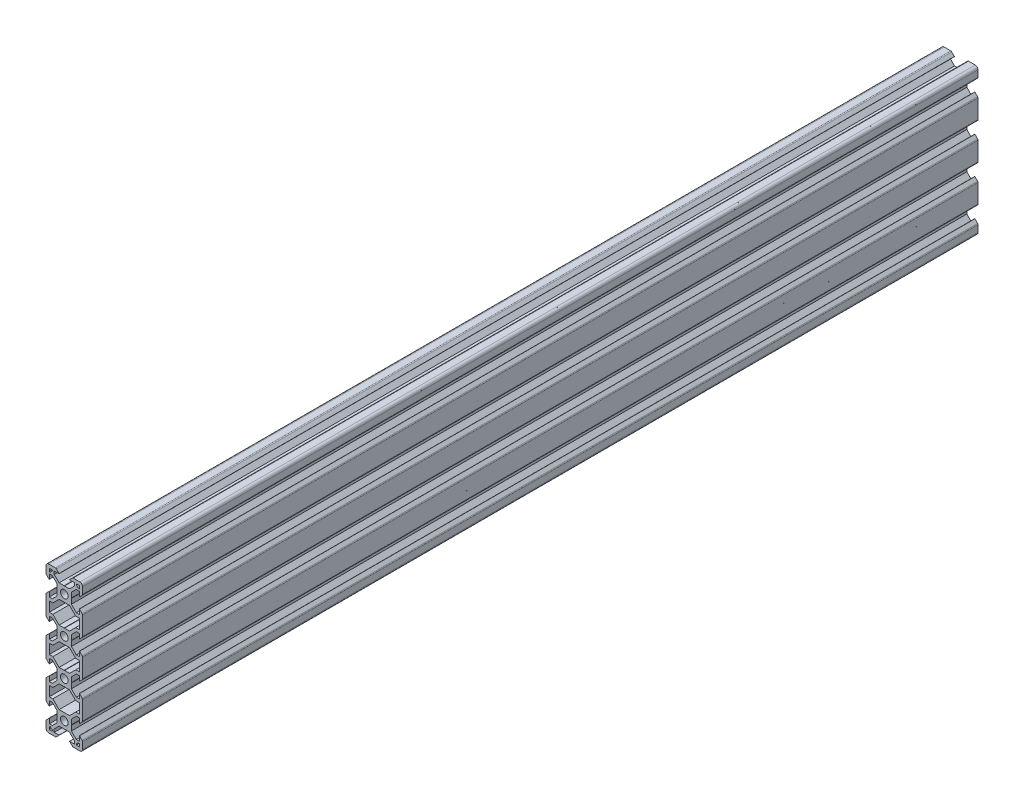
SolidWorks part; units mm, degrees
material "6063-T5"
ref_plane "Front Plane" through (0, 0, 0) normal (0, 0, 1) x (1, 0, 0)
ref_plane "Top Plane" through (0, 0, 0) normal (0, 1, 0) x (1, 0, 0)
ref_plane "Right Plane" through (0, 0, 0) normal (1, 0, 0) x (0, 0, -1)
sketch "Sketch2" plane through (0, 0, 0) normal (0, 0, 1) x (1, 0, 0)
  line L0 (-8.2, 2.8875) -> (-8.2, 5.4975)
  line L3 (-4.9072, 9.9975) -> (-8.5, 9.9975)
  line L4 (-10, 4.9047) -> (-10, 8.4975)
  line L5 (-2.1, 0) -> (-3.8, 0) construction
  line L6 (0, 3.8) -> (0, 2.1) construction
  line L7 (-0.1, 3.9) -> (-2.8404, 3.9)
  line L8 (-3.9, 0.1) -> (-3.9, 2.8383)
  line L9 (-2.89, 8.1975) -> (-5.5, 8.1975)
  line L10 (-6.57, 8.1975) -> (-6.57, 7.6575)
  line L11 (-8.2, 6.5675) -> (-7.66, 6.5675)
  line L12 (-5.5, 8.1975) -> (-5.5, 6.5588)
  line L13 (-6.56, 5.4975) -> (-8.2, 5.4975)
  line L14 (-8.2, 8.1975) -> (-1.4852, 1.4847) construction
  line L15 (-6.56, 5.4975) -> (-3.9, 2.8383)
  line L16 (-5.5, 6.5588) -> (-2.8404, 3.9)
  line L17 (-7.66, 6.5675) -> (-6.57, 7.6575)
  line L18 (-8.7302, 7.6671) -> (-0.5302, -0.5304) construction
  line L19 (-7.6698, 8.7279) -> (0.5302, 0.5304) construction
  line L20 (-8.2, 8.1975) -> (0, 0) construction
  line L21 (-8.2, 6.5675) -> (-8.2, 8.1975)
  line L22 (-8.2, -0.0025) -> (-8.2, 8.1975) construction
  line L23 (-6.57, 8.1975) -> (-8.2, 8.1975)
  line L24 (0, 8.1975) -> (-8.2, 8.1975) construction
  line L25 (-10, -0.0025) -> (-10, 9.9975) construction
  line L26 (0, 9.9975) -> (-10, 9.9975) construction
  line L27 (-2.89, 8.3075) -> (-2.89, 8.1975)
  line L29 (-8.31, 2.8875) -> (-8.2, 2.8875)
  line L30 (-4.3486, 9.7661) -> (-2.89, 8.3075)
  line L31 (-8.31, 2.8875) -> (-9.7686, 4.3461)
  line L34 (-0.1, 3.9) -> (0, 3.8)
  line L35 (-3.9, 0.1) -> (-3.8, 0)
  line L36 (-10, -20) -> (0, -20) construction
  line L37 (0, 0) -> (0, -20) construction
  line L38 (0, -3.9) -> (-2.8404, -3.9)
  line L39 (-3.8, 0) -> (-3.9, -0.1)
  line L40 (-3.9, -0.1) -> (-3.9, -2.84)
  line L41 (-2.8404, -3.9) -> (-6.25, -7.3096)
  line L42 (-3.9, -2.84) -> (-6.56, -5.5)
  line L43 (-8.21, -2.89) -> (-8.21, -5.5)
  line L44 (-6.56, 5.4975) -> (-6.56, -5.5) construction
  line L45 (-6.56, -5.5) -> (-8.21, -5.5)
  line L46 (-6.25, -7.3096) -> (-6.25, -12.7) construction
  line L47 (-6.25, -7.3096) -> (-8.21, -7.3096)
  line L48 (-8.21, -2.89) -> (-8.31, -2.89)
  line L49 (-8.31, -2.89) -> (-9.7657, -4.3457)
  line L51 (-8.21, -7.3096) -> (-8.21, -12.7)
  line L52 (-0.1, -16.1) -> (-2.85, -16.1)
  line L53 (-3.9, -17.16) -> (-3.9, -19.9)
  line L54 (-6.25, -12.7) -> (-2.85, -16.1)
  line L58 (-3.9, -17.16) -> (-6.56, -14.5)
  line L60 (-8.21, -17.11) -> (-8.31, -17.11)
  line L61 (-10, -4.9114) -> (-10, -15.0886)
  line L62 (-9.7657, -15.6543) -> (-8.31, -17.11)
  line L63 (-0.1, -16.1) -> (0, -16.2)
  line L64 (-3.9, -19.9) -> (-3.8, -20)
  line L65 (-8.21, -14.5) -> (-6.56, -14.5)
  line L66 (-8.21, -12.7) -> (-6.25, -12.7)
  line L67 (-10, -30.01) -> (0, -30.01) construction
  line L68 (-8.21, -14.5) -> (-8.21, -17.11)
  line L69 (-3.9, -20.1) -> (-3.8, -20)
  line L71 (-10, -20) -> (0, -20) construction
  line L72 (-8.21, -30.01) -> (-8.21, -27.31)
  line L73 (-10, -30.01) -> (-10, -24.9101)
  line L74 (-8.21, -25.4987) -> (-8.21, -22.8887)
  line L76 (-8.21, -27.31) -> (-6.25, -27.31)
  line L77 (-8.21, -25.4987) -> (-6.56, -25.4987)
  line L85 (-0.1, -23.9) -> (0, -23.8)
  line L95 (-9.7657, -24.3444) -> (-8.31, -22.8887)
  line L96 (-8.21, -22.8887) -> (-8.31, -22.8887)
  line L97 (-3.9, -22.8387) -> (-6.56, -25.4987)
  line L98 (-6.25, -27.31) -> (-2.84, -23.9)
  line L99 (-3.9, -22.8387) -> (-3.9, -20.1)
  line L100 (-0.1, -23.9) -> (-2.84, -23.9)
  arc A1 (-10, 8.4975) -> (-8.5, 9.9975) centre (-8.5, 8.4975) cw
  arc A2 (-9.7686, 4.3461) -> (-10, 4.9047) centre (-9.21, 4.9047) cw
  arc A3 (-4.3486, 9.7661) -> (-4.9072, 9.9975) centre (-4.9072, 9.2075) ccw
  arc A5 (0, 2.1) -> (0, -2.1) centre (0, 0) ccw
  arc A6 (-9.7657, -15.6543) -> (-10, -15.0886) centre (-9.2, -15.0886) cw
  arc A7 (-9.7657, -4.3457) -> (-10, -4.9114) centre (-9.2, -4.9114) ccw
  arc A8 (0, -17.9) -> (0, -22.1) centre (0, -20) ccw
  arc A10 (-9.7657, -24.3444) -> (-10, -24.9101) centre (-9.2, -24.9101) ccw
  point P29 (-10, 9.9975)
  point P39 (-10, 4.5775)
  point P42 (-4.58, 9.9975)
  point P76 (-10, -15.42)
  point P79 (-10, -4.58)
  dimension "D15" = 1.5
  dimension "D22" = 0.79
  dimension "D30" = 2.1
  dimension "D31" = 2.1
  dimension "D51" = 0.8
  dimension "D52" = 2.61
  dimension "D64" = 1.65
  dimension "D53" = 0.8
  dimension "D55" = 3.9
  dimension "D4" = 1.8
  dimension "D5" = 3.43
  dimension "D6" = 3.43
  dimension "D7" = 0.54
  dimension "D8" = 0.54
  dimension "D9" = 1.07
  dimension "D10" = 1.07
  dimension "D11" = 3.9
  dimension "D12" = 3.9
  dimension "D16" = 7.11
  dimension "D17" = 0.11
  dimension "D18" = 1.69
  dimension "D19" = 0.11
  dimension "D20" = 7.11
  dimension "D21" = 1.69
  dimension "D23" = 10
  dimension "D24" = 0.1
  dimension "D25" = 45
  dimension "D26" = 0.1
  dimension "D27" = 45
  dimension "D28" = 1.64
  dimension "D29" = 20
  dimension "D32" = 3.9
  dimension "D33" = 45
  dimension "D34" = 2.74
  dimension "D35" = 45
  dimension "D36" = 1.96
  dimension "D37" = 2.61
  dimension "D38" = 90
  dimension "D39" = 2.61
  dimension "D40" = 3.9
  dimension "D41" = 3.9
  dimension "D42" = 135
  dimension "D44" = 45
  dimension "D45" = 1.8
  dimension "D46" = 0.1
  dimension "D47" = 0.1
  dimension "D48" = 45
  dimension "D49" = 0.1
  dimension "D50" = 45
  dimension "D43" = 5.5
  dimension "D54" = 3.9
  dimension "D56" = 45
  dimension "D57" = 2.7
  dimension "D59" = 45
  dimension "D60" = 0.1
  dimension "D61" = 0.1
  dimension "D62" = 45
  dimension "D63" = 2.84
  dimension "D65" = 1.96
  dimension "D66" = 45
  dimension "D67" = 1.5
  dimension "D13" = 0.75
  dimension "D14" = 0.75
sketch "Sketch3" plane through (0, 0, 0) normal (0, 0, 1) x (1, 0, 0)
  line L0 (-0.1, 3.9) -> (0, 3.8) construction
  line L1 (-0.1, 3.9) -> (-2.8404, 3.9) construction
  line L2 (-5.5, 6.5588) -> (-2.8404, 3.9) construction
  line L3 (-5.5, 8.1975) -> (-5.5, 6.5588) construction
  line L4 (-2.89, 8.1975) -> (-5.5, 8.1975) construction
  line L5 (-7.66, 6.5675) -> (-6.57, 7.6575)
  line L6 (-6.57, 7.6575) -> (-6.57, 8.1975)
  line L7 (-6.57, 8.1975) -> (-8.2, 8.1975)
  line L8 (-8.2, 8.1975) -> (-8.2, 6.5675)
  line L9 (-8.2, 6.5675) -> (-7.66, 6.5675)
  line L10 (-7.66, 6.5675) -> (-6.57, 7.6575)
  line L11 (-6.57, 7.6575) -> (-6.57, 8.1975)
  line L12 (-6.57, 8.1975) -> (-8.2, 8.1975)
  line L13 (-8.2, 8.1975) -> (-8.2, 6.5675)
  line L14 (-8.2, 6.5675) -> (-7.66, 6.5675)
  line L15 (-2.89, 8.3075) -> (-2.89, 8.1975) construction
  line L16 (-4.3486, 9.7661) -> (-2.89, 8.3075) construction
  line L17 (-4.9072, 9.9975) -> (-8.5, 9.9975) construction
  line L18 (-10, 4.9047) -> (-10, 8.4975) construction
  line L19 (-8.31, 2.8875) -> (-9.7686, 4.3461) construction
  line L20 (-8.31, 2.8875) -> (-8.2, 2.8875) construction
  line L21 (-8.2, 2.8875) -> (-8.2, 5.4975) construction
  line L22 (-6.56, 5.4975) -> (-8.2, 5.4975) construction
  line L23 (-6.56, 5.4975) -> (-3.9, 2.8383) construction
  line L24 (-3.9, 0.1) -> (-3.9, 2.8383) construction
  line L25 (-3.9, 0.1) -> (-3.8, 0) construction
  line L26 (-3.8, 0) -> (-3.9, -0.1) construction
  line L27 (-3.9, -0.1) -> (-3.9, -2.84) construction
  line L28 (-3.9, -2.84) -> (-6.56, -5.5) construction
  line L29 (-6.56, -5.5) -> (-8.21, -5.5) construction
  line L30 (-8.21, -2.89) -> (-8.21, -5.5) construction
  line L31 (-8.21, -2.89) -> (-8.31, -2.89) construction
  line L32 (-8.31, -2.89) -> (-9.7657, -4.3457) construction
  line L33 (-10, -4.9114) -> (-10, -15.0886) construction
  line L34 (-9.7657, -15.6543) -> (-8.31, -17.11) construction
  line L35 (-8.21, -17.11) -> (-8.31, -17.11) construction
  line L36 (-8.21, -14.5) -> (-8.21, -17.11) construction
  line L37 (-8.21, -14.5) -> (-6.56, -14.5) construction
  line L38 (-3.9, -17.16) -> (-6.56, -14.5) construction
  line L39 (-3.9, -17.16) -> (-3.9, -19.9) construction
  line L40 (-3.9, -19.9) -> (-3.8, -20) construction
  line L41 (-3.9, -20.1) -> (-3.8, -20) construction
  line L42 (-3.9, -22.8387) -> (-3.9, -20.1) construction
  line L43 (-3.9, -22.8387) -> (-6.56, -25.4987) construction
  line L44 (-8.21, -25.4987) -> (-6.56, -25.4987) construction
  line L45 (-8.21, -25.4987) -> (-8.21, -22.8887) construction
  line L46 (-8.21, -22.8887) -> (-8.31, -22.8887) construction
  line L47 (-9.7657, -24.3444) -> (-8.31, -22.8887) construction
  line L48 (-10, -30.01) -> (-10, -24.9101) construction
  line L49 (0, -3.9) -> (-2.8404, -3.9) construction
  line L50 (-2.8404, -3.9) -> (-6.25, -7.3096) construction
  line L51 (-6.25, -7.3096) -> (-8.21, -7.3096) construction
  line L52 (-8.21, -7.3096) -> (-8.21, -12.7) construction
  line L53 (-8.21, -12.7) -> (-6.25, -12.7) construction
  line L54 (-6.25, -12.7) -> (-2.85, -16.1) construction
  line L55 (-0.1, -16.1) -> (-2.85, -16.1) construction
  line L56 (-0.1, -16.1) -> (0, -16.2) construction
  line L57 (-0.1, -23.9) -> (0, -23.8) construction
  line L58 (-0.1, -23.9) -> (-2.84, -23.9) construction
  line L59 (-6.25, -27.31) -> (-2.84, -23.9) construction
  line L60 (-8.21, -27.31) -> (-6.25, -27.31) construction
  line L61 (-8.21, -30.01) -> (-8.21, -27.31) construction
  line L62 (-0.1, 3.9) -> (0, 3.8)
  line L63 (-0.1, 3.9) -> (-2.8404, 3.9)
  line L64 (-5.5, 6.5588) -> (-2.8404, 3.9)
  line L65 (-5.5, 8.1975) -> (-5.5, 6.5588)
  line L66 (-2.89, 8.1975) -> (-5.5, 8.1975)
  line L67 (-2.89, 8.3075) -> (-2.89, 8.1975)
  line L68 (-4.3486, 9.7661) -> (-2.89, 8.3075)
  line L69 (-4.9072, 9.9975) -> (-8.5, 9.9975)
  line L70 (-10, 4.9047) -> (-10, 8.4975)
  line L71 (-8.31, 2.8875) -> (-9.7686, 4.3461)
  line L72 (-8.31, 2.8875) -> (-8.2, 2.8875)
  line L73 (-8.2, 2.8875) -> (-8.2, 5.4975)
  line L74 (-6.56, 5.4975) -> (-8.2, 5.4975)
  line L75 (-6.56, 5.4975) -> (-3.9, 2.8383)
  line L76 (-3.9, 0.1) -> (-3.9, 2.8383)
  line L77 (-3.9, 0.1) -> (-3.8, 0)
  line L78 (-3.8, 0) -> (-3.9, -0.1)
  line L79 (-3.9, -0.1) -> (-3.9, -2.84)
  line L80 (-3.9, -2.84) -> (-6.56, -5.5)
  line L81 (-6.56, -5.5) -> (-8.21, -5.5)
  line L82 (-8.21, -2.89) -> (-8.21, -5.5)
  line L83 (-8.21, -2.89) -> (-8.31, -2.89)
  line L84 (-8.31, -2.89) -> (-9.7657, -4.3457)
  line L85 (-10, -4.9114) -> (-10, -15.0886)
  line L86 (-9.7657, -15.6543) -> (-8.31, -17.11)
  line L87 (-8.21, -17.11) -> (-8.31, -17.11)
  line L88 (-8.21, -14.5) -> (-8.21, -17.11)
  line L89 (-8.21, -14.5) -> (-6.56, -14.5)
  line L90 (-3.9, -17.16) -> (-6.56, -14.5)
  line L91 (-3.9, -17.16) -> (-3.9, -19.9)
  line L92 (-3.9, -19.9) -> (-3.8, -20)
  line L93 (-3.9, -20.1) -> (-3.8, -20)
  line L94 (-3.9, -22.8387) -> (-3.9, -20.1)
  line L95 (-3.9, -22.8387) -> (-6.56, -25.4987)
  line L96 (-8.21, -25.4987) -> (-6.56, -25.4987)
  line L97 (-8.21, -25.4987) -> (-8.21, -22.8887)
  line L98 (-8.21, -22.8887) -> (-8.31, -22.8887)
  line L99 (-9.7657, -24.3444) -> (-8.31, -22.8887)
  line L100 (-10, -35.1099) -> (-10, -24.9101)
  line L101 (2.8404, -3.9) -> (-2.8404, -3.9)
  line L102 (-2.8404, -3.9) -> (-6.25, -7.3096)
  line L103 (-6.25, -7.3096) -> (-8.21, -7.3096)
  line L104 (-8.21, -7.3096) -> (-8.21, -12.7)
  line L105 (-8.21, -12.7) -> (-6.25, -12.7)
  line L106 (-6.25, -12.7) -> (-2.85, -16.1)
  line L107 (-0.1, -16.1) -> (-2.85, -16.1)
  line L108 (-0.1, -16.1) -> (0, -16.2)
  line L109 (-0.1, -23.9) -> (0, -23.8)
  line L110 (-0.1, -23.9) -> (-2.84, -23.9)
  line L111 (-6.25, -27.31) -> (-2.84, -23.9)
  line L112 (-8.21, -27.31) -> (-6.25, -27.31)
  line L113 (-8.21, -32.71) -> (-8.21, -27.31)
  line L114 (0, 0) -> (0, -20) construction
  line L115 (-10, -30.01) -> (0, -30.01) construction
  line L116 (0, 0) -> (0, -20) construction
  line L117 (-10, -30.01) -> (10, -30.01) construction
  line L118 (8.21, -32.71) -> (8.21, -27.31)
  line L119 (8.21, -27.31) -> (6.25, -27.31)
  line L120 (6.25, -27.31) -> (2.84, -23.9)
  line L121 (0.1, -23.9) -> (2.84, -23.9)
  line L122 (0.1, -23.9) -> (0, -23.8)
  line L123 (0.1, -16.1) -> (0, -16.2)
  line L124 (0.1, -16.1) -> (2.85, -16.1)
  line L125 (6.25, -12.7) -> (2.85, -16.1)
  line L126 (8.21, -12.7) -> (6.25, -12.7)
  line L127 (8.21, -7.3096) -> (8.21, -12.7)
  line L128 (6.25, -7.3096) -> (8.21, -7.3096)
  line L129 (2.8404, -3.9) -> (6.25, -7.3096)
  line L130 (10, -35.1099) -> (10, -24.9101)
  line L131 (9.7657, -24.3444) -> (8.31, -22.8887)
  line L132 (8.21, -22.8887) -> (8.31, -22.8887)
  line L133 (8.21, -25.4987) -> (8.21, -22.8887)
  line L134 (8.21, -25.4987) -> (6.56, -25.4987)
  line L135 (3.9, -22.8387) -> (6.56, -25.4987)
  line L136 (3.9, -22.8387) -> (3.9, -20.1)
  line L137 (3.9, -20.1) -> (3.8, -20)
  line L138 (3.9, -19.9) -> (3.8, -20)
  line L139 (3.9, -17.16) -> (3.9, -19.9)
  line L140 (3.9, -17.16) -> (6.56, -14.5)
  line L141 (8.21, -14.5) -> (6.56, -14.5)
  line L142 (8.21, -14.5) -> (8.21, -17.11)
  line L143 (8.21, -17.11) -> (8.31, -17.11)
  line L144 (9.7657, -15.6543) -> (8.31, -17.11)
  line L145 (10, -4.9114) -> (10, -15.0886)
  line L146 (8.31, -2.89) -> (9.7657, -4.3457)
  line L147 (8.21, -2.89) -> (8.31, -2.89)
  line L148 (8.21, -2.89) -> (8.21, -5.5)
  line L149 (6.56, -5.5) -> (8.21, -5.5)
  line L150 (3.9, -2.84) -> (6.56, -5.5)
  line L151 (3.9, -0.1) -> (3.9, -2.84)
  line L152 (3.8, 0) -> (3.9, -0.1)
  line L153 (3.9, 0.1) -> (3.8, 0)
  line L154 (3.9, 0.1) -> (3.9, 2.8383)
  line L155 (6.56, 5.4975) -> (3.9, 2.8383)
  line L156 (6.56, 5.4975) -> (8.2, 5.4975)
  line L157 (8.2, 2.8875) -> (8.2, 5.4975)
  line L158 (8.31, 2.8875) -> (8.2, 2.8875)
  line L159 (8.31, 2.8875) -> (9.7686, 4.3461)
  line L160 (10, 4.9047) -> (10, 8.4975)
  line L161 (4.9072, 9.9975) -> (8.5, 9.9975)
  line L162 (4.3486, 9.7661) -> (2.89, 8.3075)
  line L163 (2.89, 8.3075) -> (2.89, 8.1975)
  line L164 (2.89, 8.1975) -> (5.5, 8.1975)
  line L165 (5.5, 8.1975) -> (5.5, 6.5588)
  line L166 (5.5, 6.5588) -> (2.8404, 3.9)
  line L167 (0.1, 3.9) -> (2.8404, 3.9)
  line L168 (0.1, 3.9) -> (0, 3.8)
  line L169 (8.2, 6.5675) -> (7.66, 6.5675)
  line L170 (8.2, 8.1975) -> (8.2, 6.5675)
  line L171 (6.57, 8.1975) -> (8.2, 8.1975)
  line L172 (6.57, 7.6575) -> (6.57, 8.1975)
  line L173 (7.66, 6.5675) -> (6.57, 7.6575)
  line L174 (0, -60.02) -> (0, -40.02) construction
  line L175 (7.66, -66.5875) -> (6.57, -67.6775)
  line L176 (6.57, -67.6775) -> (6.57, -68.2175)
  line L177 (6.57, -68.2175) -> (8.2, -68.2175)
  line L178 (8.2, -68.2175) -> (8.2, -66.5875)
  line L179 (8.2, -66.5875) -> (7.66, -66.5875)
  line L180 (0.1, -63.92) -> (0, -63.82)
  line L181 (0.1, -63.92) -> (2.8404, -63.92)
  line L182 (5.5, -66.5788) -> (2.8404, -63.92)
  line L183 (5.5, -68.2175) -> (5.5, -66.5788)
  line L184 (2.89, -68.2175) -> (5.5, -68.2175)
  line L185 (2.89, -68.3275) -> (2.89, -68.2175)
  line L186 (4.3486, -69.7861) -> (2.89, -68.3275)
  line L187 (4.9072, -70.0175) -> (8.5, -70.0175)
  line L188 (10, -64.9247) -> (10, -68.5175)
  line L189 (8.31, -62.9075) -> (9.7686, -64.3661)
  line L190 (8.31, -62.9075) -> (8.2, -62.9075)
  line L191 (8.2, -62.9075) -> (8.2, -65.5175)
  line L192 (6.56, -65.5175) -> (8.2, -65.5175)
  line L193 (6.56, -65.5175) -> (3.9, -62.8583)
  line L194 (3.9, -60.12) -> (3.9, -62.8583)
  line L195 (3.9, -60.12) -> (3.8, -60.02)
  line L196 (3.8, -60.02) -> (3.9, -59.92)
  line L197 (3.9, -59.92) -> (3.9, -57.18)
  line L198 (3.9, -57.18) -> (6.56, -54.52)
  line L199 (6.56, -54.52) -> (8.21, -54.52)
  line L200 (8.21, -57.13) -> (8.21, -54.52)
  line L201 (8.21, -57.13) -> (8.31, -57.13)
  line L202 (8.31, -57.13) -> (9.7657, -55.6743)
  line L203 (10, -55.1086) -> (10, -44.9314)
  line L204 (9.7657, -44.3657) -> (8.31, -42.91)
  line L205 (8.21, -42.91) -> (8.31, -42.91)
  line L206 (8.21, -45.52) -> (8.21, -42.91)
  line L207 (8.21, -45.52) -> (6.56, -45.52)
  line L208 (3.9, -42.86) -> (6.56, -45.52)
  line L209 (3.9, -42.86) -> (3.9, -40.12)
  line L210 (3.9, -40.12) -> (3.8, -40.02)
  line L211 (3.9, -39.92) -> (3.8, -40.02)
  line L212 (3.9, -37.1813) -> (3.9, -39.92)
  line L213 (3.9, -37.1813) -> (6.56, -34.5213)
  line L214 (8.21, -34.5213) -> (6.56, -34.5213)
  line L215 (8.21, -34.5213) -> (8.21, -37.1313)
  line L216 (8.21, -37.1313) -> (8.31, -37.1313)
  line L217 (9.7657, -35.6756) -> (8.31, -37.1313)
  line L218 (2.8404, -56.12) -> (6.25, -52.7104)
  line L219 (6.25, -52.7104) -> (8.21, -52.7104)
  line L220 (8.21, -52.7104) -> (8.21, -47.32)
  line L221 (8.21, -47.32) -> (6.25, -47.32)
  line L222 (6.25, -47.32) -> (2.85, -43.92)
  line L223 (0.1, -43.92) -> (2.85, -43.92)
  line L224 (0.1, -43.92) -> (0, -43.82)
  line L225 (0.1, -36.12) -> (0, -36.22)
  line L226 (0.1, -36.12) -> (2.84, -36.12)
  line L227 (6.25, -32.71) -> (2.84, -36.12)
  line L228 (8.21, -32.71) -> (6.25, -32.71)
  line L229 (-8.21, -32.71) -> (-6.25, -32.71)
  line L230 (-6.25, -32.71) -> (-2.84, -36.12)
  line L231 (-0.1, -36.12) -> (-2.84, -36.12)
  line L232 (-0.1, -36.12) -> (0, -36.22)
  line L233 (-0.1, -43.92) -> (0, -43.82)
  line L234 (-0.1, -43.92) -> (-2.85, -43.92)
  line L235 (-6.25, -47.32) -> (-2.85, -43.92)
  line L236 (-8.21, -47.32) -> (-6.25, -47.32)
  line L237 (-8.21, -52.7104) -> (-8.21, -47.32)
  line L238 (-6.25, -52.7104) -> (-8.21, -52.7104)
  line L239 (-2.8404, -56.12) -> (-6.25, -52.7104)
  line L240 (2.8404, -56.12) -> (-2.8404, -56.12)
  line L241 (-9.7657, -35.6756) -> (-8.31, -37.1313)
  line L242 (-8.21, -37.1313) -> (-8.31, -37.1313)
  line L243 (-8.21, -34.5213) -> (-8.21, -37.1313)
  line L244 (-8.21, -34.5213) -> (-6.56, -34.5213)
  line L245 (-3.9, -37.1813) -> (-6.56, -34.5213)
  line L246 (-3.9, -37.1813) -> (-3.9, -39.92)
  line L247 (-3.9, -39.92) -> (-3.8, -40.02)
  line L248 (-3.9, -40.12) -> (-3.8, -40.02)
  line L249 (-3.9, -42.86) -> (-3.9, -40.12)
  line L250 (-3.9, -42.86) -> (-6.56, -45.52)
  line L251 (-8.21, -45.52) -> (-6.56, -45.52)
  line L252 (-8.21, -45.52) -> (-8.21, -42.91)
  line L253 (-8.21, -42.91) -> (-8.31, -42.91)
  line L254 (-9.7657, -44.3657) -> (-8.31, -42.91)
  line L255 (-10, -55.1086) -> (-10, -44.9314)
  line L256 (-8.31, -57.13) -> (-9.7657, -55.6743)
  line L257 (-8.21, -57.13) -> (-8.31, -57.13)
  line L258 (-8.21, -57.13) -> (-8.21, -54.52)
  line L259 (-6.56, -54.52) -> (-8.21, -54.52)
  line L260 (-3.9, -57.18) -> (-6.56, -54.52)
  line L261 (-3.9, -59.92) -> (-3.9, -57.18)
  line L262 (-3.8, -60.02) -> (-3.9, -59.92)
  line L263 (-3.9, -60.12) -> (-3.8, -60.02)
  line L264 (-3.9, -60.12) -> (-3.9, -62.8583)
  line L265 (-6.56, -65.5175) -> (-3.9, -62.8583)
  line L266 (-6.56, -65.5175) -> (-8.2, -65.5175)
  line L267 (-8.2, -62.9075) -> (-8.2, -65.5175)
  line L268 (-8.31, -62.9075) -> (-8.2, -62.9075)
  line L269 (-8.31, -62.9075) -> (-9.7686, -64.3661)
  line L270 (-10, -64.9247) -> (-10, -68.5175)
  line L271 (-4.9072, -70.0175) -> (-8.5, -70.0175)
  line L272 (-4.3486, -69.7861) -> (-2.89, -68.3275)
  line L273 (-2.89, -68.3275) -> (-2.89, -68.2175)
  line L274 (-2.89, -68.2175) -> (-5.5, -68.2175)
  line L275 (-5.5, -68.2175) -> (-5.5, -66.5788)
  line L276 (-5.5, -66.5788) -> (-2.8404, -63.92)
  line L277 (-0.1, -63.92) -> (-2.8404, -63.92)
  line L278 (-0.1, -63.92) -> (0, -63.82)
  line L279 (-8.2, -66.5875) -> (-7.66, -66.5875)
  line L280 (-8.2, -68.2175) -> (-8.2, -66.5875)
  line L281 (-6.57, -68.2175) -> (-8.2, -68.2175)
  line L282 (-6.57, -67.6775) -> (-6.57, -68.2175)
  line L283 (-7.66, -66.5875) -> (-6.57, -67.6775)
  arc A0 (0, 2.1) -> (0, -2.1) centre (0, 0) ccw construction
  arc A1 (0, -17.9) -> (0, -22.1) centre (0, -20) ccw construction
  arc A2 (-4.3486, 9.7661) -> (-4.9072, 9.9975) centre (-4.9072, 9.2075) ccw construction
  arc A3 (-8.5, 9.9975) -> (-10, 8.4975) centre (-8.5, 8.4975) ccw construction
  arc A4 (-10, 4.9047) -> (-9.7686, 4.3461) centre (-9.21, 4.9047) ccw construction
  arc A5 (-9.7657, -4.3457) -> (-10, -4.9114) centre (-9.2, -4.9114) ccw construction
  arc A6 (-10, -15.0886) -> (-9.7657, -15.6543) centre (-9.2, -15.0886) ccw construction
  arc A7 (-9.7657, -24.3444) -> (-10, -24.9101) centre (-9.2, -24.9101) ccw construction
  circle A8 centre (0, 0) radius 2.1
  circle A9 centre (0, -20) radius 2.1
  arc A10 (-4.3486, 9.7661) -> (-4.9072, 9.9975) centre (-4.9072, 9.2075) ccw
  arc A11 (-8.5, 9.9975) -> (-10, 8.4975) centre (-8.5, 8.4975) ccw
  arc A12 (-10, 4.9047) -> (-9.7686, 4.3461) centre (-9.21, 4.9047) ccw
  arc A13 (-9.7657, -4.3457) -> (-10, -4.9114) centre (-9.2, -4.9114) ccw
  arc A14 (-10, -15.0886) -> (-9.7657, -15.6543) centre (-9.2, -15.0886) ccw
  arc A15 (-9.7657, -24.3444) -> (-10, -24.9101) centre (-9.2, -24.9101) ccw
  arc A16 (9.7657, -24.3444) -> (10, -24.9101) centre (9.2, -24.9101) cw
  arc A17 (10, -15.0886) -> (9.7657, -15.6543) centre (9.2, -15.0886) cw
  arc A18 (9.7657, -4.3457) -> (10, -4.9114) centre (9.2, -4.9114) cw
  arc A19 (10, 4.9047) -> (9.7686, 4.3461) centre (9.21, 4.9047) cw
  arc A20 (8.5, 9.9975) -> (10, 8.4975) centre (8.5, 8.4975) cw
  arc A21 (4.3486, 9.7661) -> (4.9072, 9.9975) centre (4.9072, 9.2075) cw
  arc A22 (4.3486, -69.7861) -> (4.9072, -70.0175) centre (4.9072, -69.2275) ccw
  arc A23 (8.5, -70.0175) -> (10, -68.5175) centre (8.5, -68.5175) ccw
  arc A24 (10, -64.9247) -> (9.7686, -64.3661) centre (9.21, -64.9247) ccw
  arc A25 (9.7657, -55.6743) -> (10, -55.1086) centre (9.2, -55.1086) ccw
  arc A26 (10, -44.9314) -> (9.7657, -44.3657) centre (9.2, -44.9314) ccw
  arc A27 (9.7657, -35.6756) -> (10, -35.1099) centre (9.2, -35.1099) ccw
  arc A28 (-9.7657, -35.6756) -> (-10, -35.1099) centre (-9.2, -35.1099) cw
  arc A29 (-10, -44.9314) -> (-9.7657, -44.3657) centre (-9.2, -44.9314) cw
  arc A30 (-9.7657, -55.6743) -> (-10, -55.1086) centre (-9.2, -55.1086) cw
  arc A31 (-10, -64.9247) -> (-9.7686, -64.3661) centre (-9.21, -64.9247) cw
  arc A32 (-8.5, -70.0175) -> (-10, -68.5175) centre (-8.5, -68.5175) cw
  arc A33 (-4.3486, -69.7861) -> (-4.9072, -70.0175) centre (-4.9072, -69.2275) cw
  circle A34 centre (0, -40.02) radius 2.1
  circle A35 centre (0, -60.02) radius 2.1
  point P240 (8.21, -30.01)
  point P288 (-0.1, 9.9975)
  point P289 (0, -70.0175)
  point P290 (-10, -60.02)
  point P291 (10, -60.02)
  point P292 (10, -40.02)
  point P293 (-10, -40.02)
  point P294 (-10, -20)
  point P295 (10, -20)
  point P296 (10, 0)
  point P297 (-10, 0)
  point P298 (-45.6583, 8.4975)
  dimension "D1" = 0
extrude "Boss-Extrude1" add sketch "Sketch3" against normal mid plane 489.5
ref_plane "CenterPlane" through (0, -30.01, 0) normal (0, 1, 0) x (1, 0, 0)
